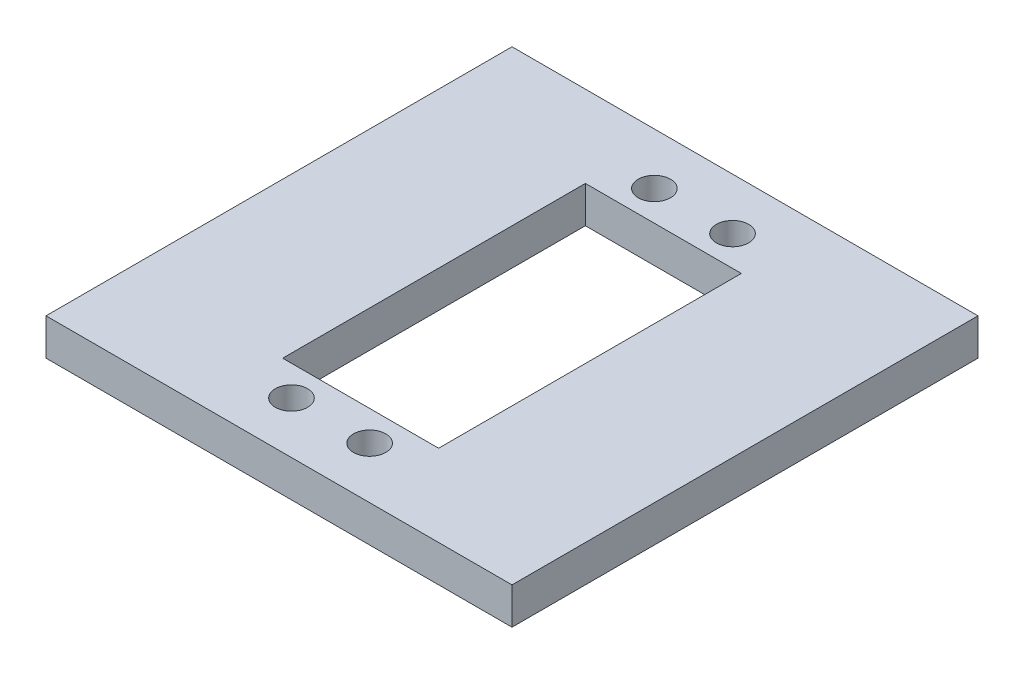
SolidWorks part; units mm, degrees
ref_plane "Front Plane" through (0, 0, 0) normal (0, 0, 1) x (1, 0, 0)
ref_plane "Top Plane" through (0, 0, 0) normal (0, 1, 0) x (1, 0, 0)
ref_plane "Right Plane" through (0, 0, 0) normal (1, 0, 0) x (0, 0, -1)
sketch "Sketch2" plane through (0, 0, 0) normal (0, 1, 0) x (1, 0, 0)
  line L1 (-31.75, -31.75) -> (31.75, -31.75)
  line L2 (-31.75, -31.75) -> (-31.75, 31.75)
  line L3 (-31.75, 31.75) -> (31.75, 31.75)
  line L4 (31.75, -31.75) -> (31.75, 31.75)
  line L5 (-31.75, -31.75) -> (31.75, 31.75) construction
  line L6 (-31.75, 31.75) -> (31.75, -31.75) construction
  point P0 (0, 0)
  dimension "D1" = 63.5
  dimension "D2" = 63.5
extrude "Boss-Extrude1" add sketch "Sketch2" along normal blind 5
sketch "Sketch3" plane through (0, 5, 0) normal (0, 1, 0) x (1, 0, 0)
  line L0 (0, 20.625) -> (0, 29.2674) construction
  line L1 (-10.625, -20.625) -> (10.625, -20.625)
  line L2 (-10.625, -20.625) -> (-10.625, 20.625)
  line L3 (-10.625, 20.625) -> (10.625, 20.625)
  line L4 (10.625, -20.625) -> (10.625, 20.625)
  line L5 (-10.625, -20.625) -> (10.625, 20.625) construction
  line L6 (-10.625, 20.625) -> (10.625, -20.625) construction
  line L7 (0, 0) -> (-4.9591, 0) construction
  circle A0 centre (5.325, 24.725) radius 2.2
  circle A1 centre (-5.325, 24.725) radius 2.2
  circle A2 centre (5.325, -24.725) radius 2.2
  circle A3 centre (-5.325, -24.725) radius 2.2
  point P0 (0, 0)
  dimension "D5" = 4.4
  dimension "D1" = 21.25
  dimension "D2" = 41.25
  dimension "D3" = 4.1
  dimension "D4" = 5.3
extrude "Cut-Extrude1" cut sketch "Sketch3" against normal through all
